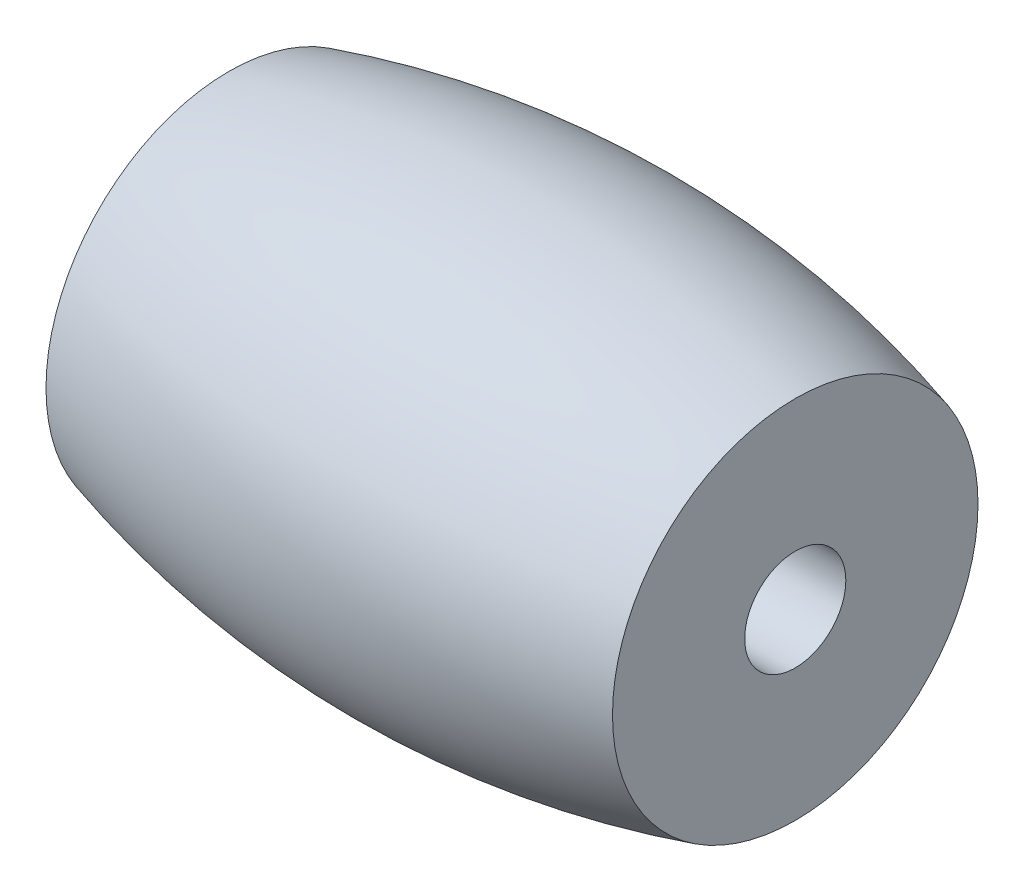
SolidWorks part; units mm, degrees
material "BUTYL"
ref_plane "前视基准面" through (0, 0, 0) normal (0, 0, 1) x (1, 0, 0)
ref_plane "上视基准面" through (0, 0, 0) normal (0, 1, 0) x (1, 0, 0)
ref_plane "右视基准面" through (0, 0, 0) normal (1, 0, 0) x (0, 0, -1)
sketch "草图1" plane through (0, 0, 0) normal (0, 0, 1) x (1, 0, 0)
  line L0 (7, 19.9) -> (-7, 19.9)
  line L3 (7, 15.3836) -> (7, 19.9)
  line L4 (-7, 15.3836) -> (-7, 19.9)
  arc A3 (-7, 15.3836) -> (7, 15.3836) centre (0, 39.8) ccw
revolve "旋转1" add sketch "草图1" angle 360 about L0
sketch "草图2" plane through (7, 0, 0) normal (1, 0, 0) x (0, 0, -1)
  circle A0 centre (0, 19.9) radius 1.25
  dimension "D1" = 2.5
extrude "切除-拉伸1" cut sketch "草图2" against normal blind 18
